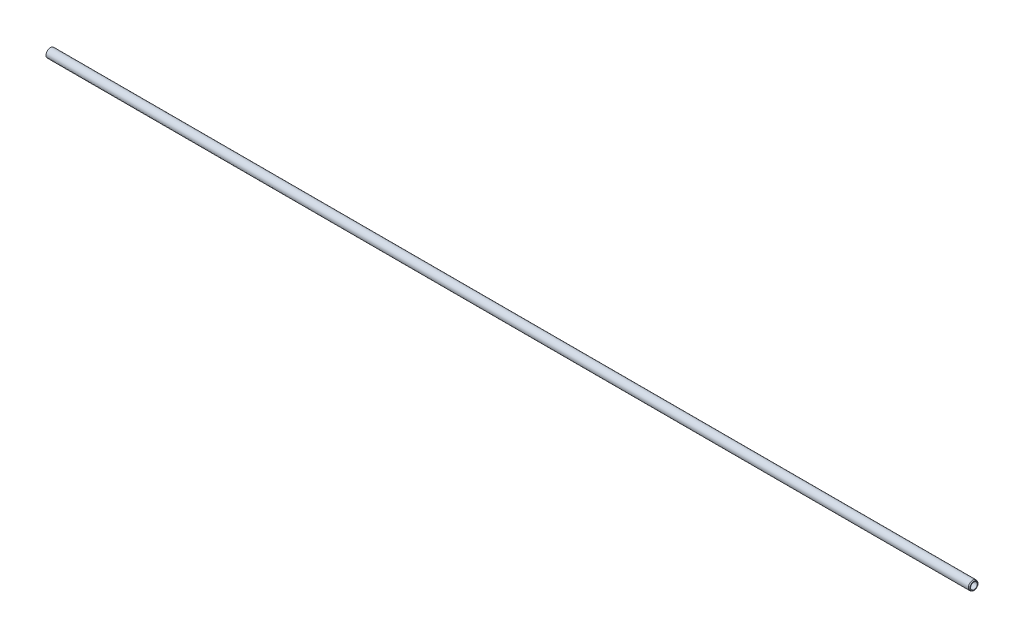
SolidWorks part; units mm, degrees
ref_plane "Front" through (0, 0, 0) normal (0, 0, 1) x (1, 0, 0)
ref_plane "Top" through (0, 0, 0) normal (0, 1, 0) x (1, 0, 0)
ref_plane "Right" through (0, 0, 0) normal (1, 0, 0) x (0, 0, -1)
sketch "Sketch1" plane through (0, 0, 0) normal (0, 0, 1) x (1, 0, 0)
  line L0 (0, 0) -> (1352.4571, 0) construction
  line L1 (0, 10) -> (0, 7.5)
  line L2 (0, 7.5) -> (2073, 7.5)
  line L4 (0, 10) -> (2070.5, 10)
  line L6 (2070.5, 10) -> (2073, 9.0901)
  line L7 (2073, 9.0901) -> (2073, 7.5)
  dimension "D1" = 20
  dimension "D2" = 15
  dimension "D3" = 20
  dimension "D4" = 2.5
  dimension "D6" = 2073
revolve "Base-Revolve" add sketch "Sketch1" angle 360 about L0
